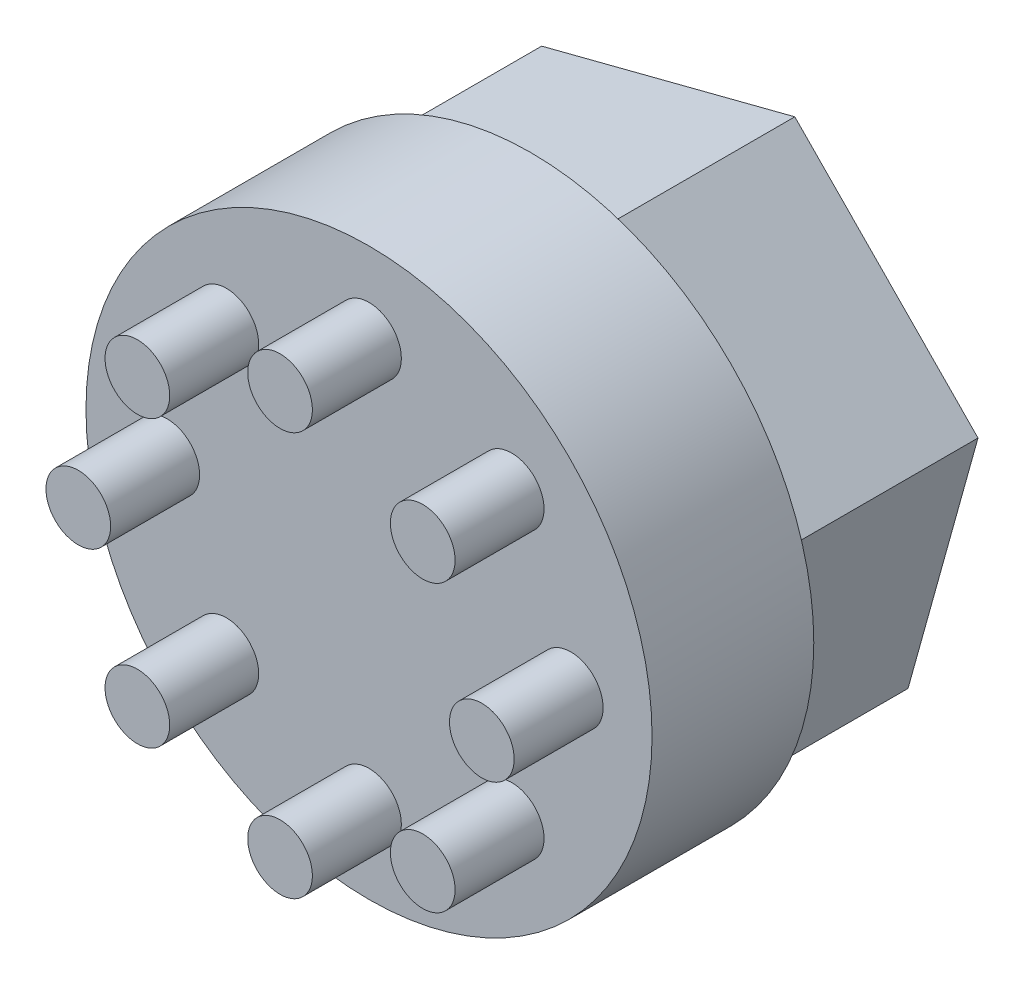
SolidWorks part; units mm, degrees
ref_plane "Plan de face" through (0, 0, 0) normal (0, 0, 1) x (1, 0, 0)
ref_plane "Plan de dessus" through (0, 0, 0) normal (0, 1, 0) x (1, 0, 0)
ref_plane "Plan de droite" through (0, 0, 0) normal (1, 0, 0) x (0, 0, -1)
sketch "Esquisse1" plane through (0, 0, 0) normal (0, 0, 1) x (1, 0, 0)
  circle A0 centre (0, 0) radius 17.5
  dimension "D1" = 35
extrude "Boss.-Extru.1" add sketch "Esquisse1" along normal blind 10
sketch "Esquisse2" plane through (0, 0, 10) normal (0, 0, 1) x (1, 0, 0)
  line L0 (0, -7.4151) -> (0, 22.91) construction
  line L1 (-5.5378, 0) -> (12.8145, 0) construction
  circle A0 centre (8.8212, 8.8212) radius 2
  circle A1 centre (0, 12.475) radius 2
  circle A2 centre (12.475, 0) radius 2
  circle A3 centre (8.8212, -8.8212) radius 2
  circle A4 centre (0, -12.475) radius 2
  circle A5 centre (-8.8212, -8.8212) radius 2
  circle A6 centre (-12.475, 0) radius 2
  circle A7 centre (-8.8212, 8.8212) radius 2
  point P24 (0, 0)
  dimension "D1" = 12.475
  dimension "D2" = 4
  dimension "D3" = 8
extrude "Boss.-Extru.2" add sketch "Esquisse2" along normal blind 5.5
sketch "Esquisse3" plane through (0, 0, 0) normal (0, 0, -1) x (-1, 0, 0)
  line L1 (11.3256, 11.5354) -> (-4.3271, 15.5759)
  line L2 (-4.3271, 15.5759) -> (-15.6527, 4.0406)
  line L3 (-15.6527, 4.0406) -> (-11.3256, -11.5354)
  line L4 (-11.3256, -11.5354) -> (4.3271, -15.5759)
  line L5 (4.3271, -15.5759) -> (15.6527, -4.0406)
  line L6 (15.6527, -4.0406) -> (11.3256, 11.5354)
  circle A0 centre (0, 0) radius 14 construction
  point P1 (3.4992, 13.5556)
  dimension "D1" = 28
extrude "Boss.-Extru.3" add sketch "Esquisse3" along normal blind 12
